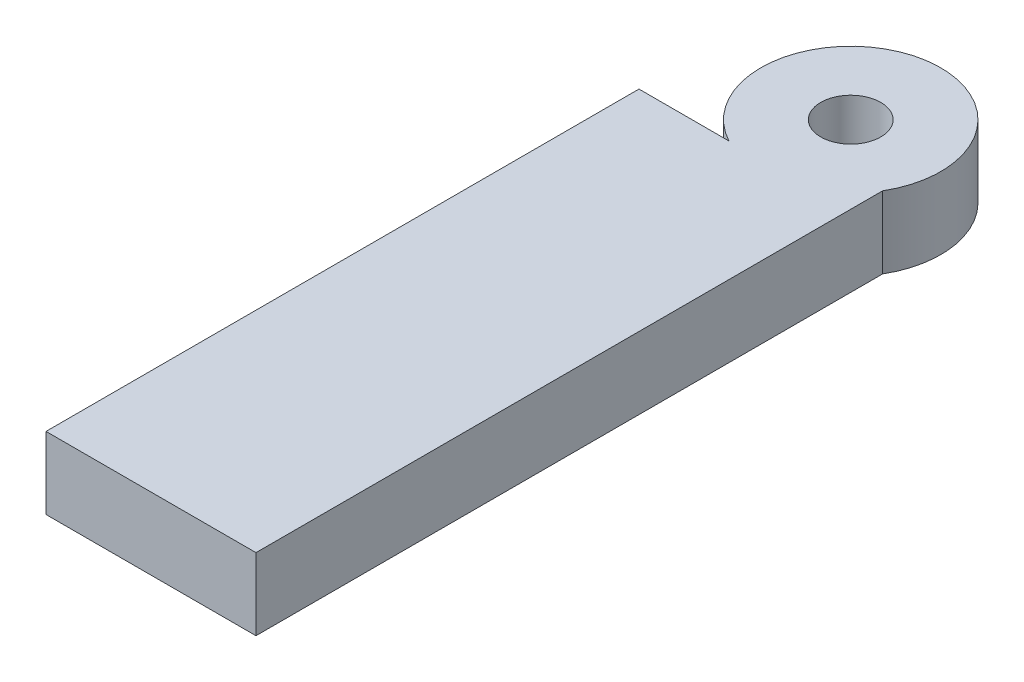
SolidWorks part; units mm, degrees
ref_plane "Front Plane" through (0, 0, 0) normal (0, 0, 1) x (1, 0, 0)
ref_plane "Top Plane" through (0, 0, 0) normal (0, 1, 0) x (1, 0, 0)
ref_plane "Right Plane" through (0, 0, 0) normal (1, 0, 0) x (0, 0, -1)
sketch "Sketch1" plane through (0, 0, 0) normal (0, 1, 0) x (1, 0, 0)
  line L0 (0, 9.525) -> (-4.4901, 5.0349)
  line L1 (0, 9.525) -> (0, 0) construction
  line L2 (-4.4901, -71.1651) -> (8.2099, -71.1651)
  line L3 (-4.4901, 5.0349) -> (-4.4901, -71.1651)
  line L4 (8.2099, -71.1651) -> (8.2099, -4.8295)
  circle A0 centre (0, 0) radius 3.175
  circle A1 centre (0, 0) radius 9.525
  dimension "D1" = 6.35
  dimension "D2" = 19.05
  dimension "D3" = 45
  dimension "D4" = 6.35
  dimension "D5" = 76.2
  dimension "D6" = 12.7
extrude "Boss-Extrude1" add sketch "Sketch1" along normal blind 7.62
sketch "Sketch2" plane through (-4.4901, 0, 0) normal (-1, 0, 0) x (0, 0, 1)
  line L1 (8.4003, 7.62) -> (71.1651, 7.62) construction
  line L2 (8.4003, 7.62) -> (8.4003, 0) construction
  circle A0 centre (14.7503, 3.81) radius 2.54
  circle A1 centre (52.8503, 3.81) radius 2.54
  dimension "D1" = 5.08
  dimension "D2" = 5.08
  dimension "D3" = 6.35
  dimension "D4" = 3.81
  dimension "D5" = 38.1
extrude "Cut-Extrude1" cut sketch "Sketch2" against normal blind 6.35
sketch "Sketch3" plane through (-4.4901, 0, 0) normal (-1, 0, 0) x (0, 0, 1)
  line L4 (8.4003, 0) -> (71.1651, 0)
  line L5 (71.1651, 0) -> (71.1651, 7.62)
  line L6 (71.1651, 7.62) -> (8.4003, 7.62)
  line L7 (8.4003, 7.62) -> (8.4003, 0)
  line L8 (8.4003, 0) -> (71.1651, 0)
  line L9 (71.1651, 0) -> (71.1651, 7.62)
  line L10 (71.1651, 7.62) -> (8.4003, 7.62)
  line L12 (8.4003, 7.62) -> (8.4003, 0)
  circle A0 centre (52.8503, 3.81) radius 2.54 construction
  circle A1 centre (14.7503, 3.81) radius 2.54 construction
  circle A2 centre (52.8503, 3.81) radius 2.54
  circle A3 centre (14.7503, 3.81) radius 2.54
  dimension "D1" = 0
extrude "Boss-Extrude2" add sketch "Sketch3" along normal blind 9.525
sketch "Sketch4" plane through (-17.9605, 0, 0) normal (-1, 0, 0) x (0, 0, 1)
  line L4 (8.4355, 0) -> (59.2355, 0)
  line L5 (59.2355, 0) -> (59.2355, 7.62)
  line L6 (59.2355, 7.62) -> (8.4355, 7.62)
  line L7 (8.4355, 7.62) -> (8.4355, 0)
  line L8 (8.4355, 0) -> (59.2355, 0)
  line L9 (59.2355, 0) -> (59.2355, 7.62)
  line L10 (59.2355, 7.62) -> (8.4355, 7.62)
  line L11 (8.4355, 7.62) -> (8.4355, 0)
  circle A0 centre (52.8503, 3.81) radius 2.54 construction
  circle A1 centre (14.7503, 3.81) radius 2.54 construction
  circle A2 centre (52.8503, 3.81) radius 2.54
  circle A3 centre (14.7503, 3.81) radius 2.54
  dimension "D1" = 0
extrude "Boss-Extrude3" [suppressed] add sketch "Sketch4" along normal blind 4.7625
